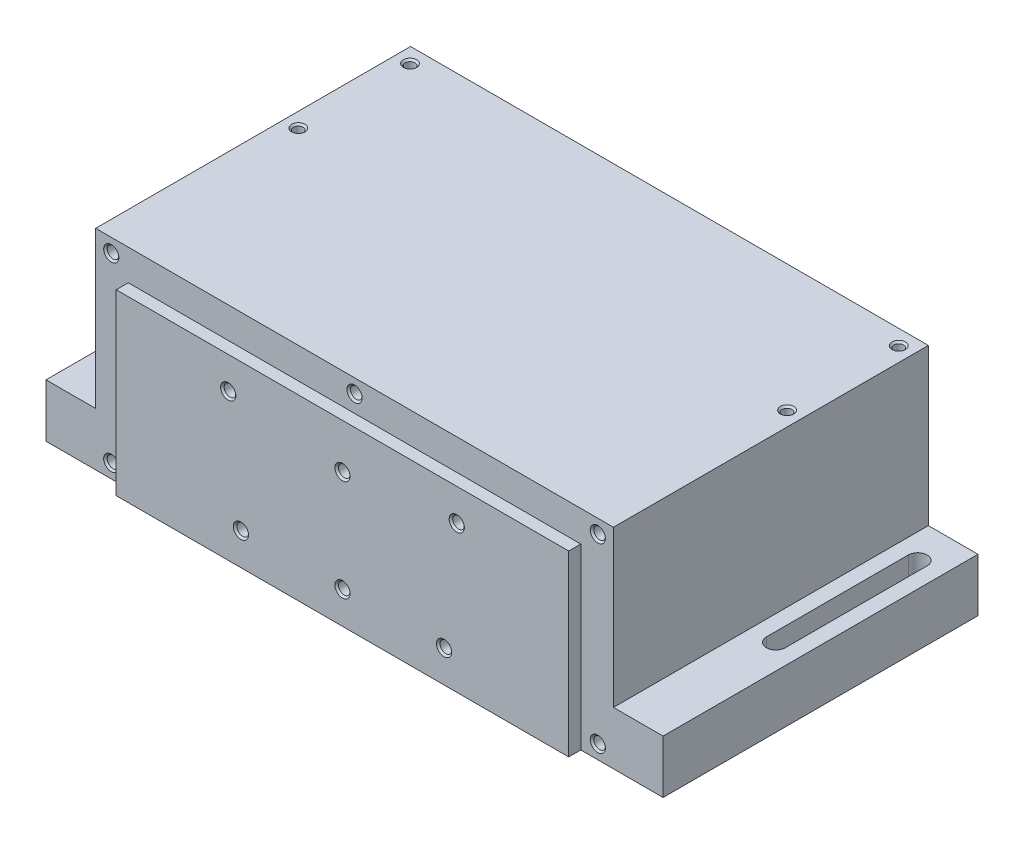
SolidWorks part; units mm, degrees
material "6061-T6 Al"
ref_plane "Front" through (0, 0, 0) normal (0, 0, 1) x (1, 0, 0)
ref_plane "Top" through (0, 0, 0) normal (0, 1, 0) x (1, 0, 0)
ref_plane "Right" through (0, 0, 0) normal (1, 0, 0) x (0, 0, -1)
sketch "Sketch1" plane through (0, 0, 0) normal (0, 0, 1) x (1, 0, 0)
  line L0 (-92.71, 2.54) -> (92.71, 2.54)
  line L1 (92.71, 2.54) -> (92.71, 0)
  line L2 (92.71, 0) -> (110.49, 0)
  line L3 (110.49, 0) -> (110.49, 19.05)
  line L4 (110.49, 19.05) -> (92.71, 19.05)
  line L5 (92.71, 19.05) -> (92.71, 74.93)
  line L6 (92.71, 74.93) -> (-92.71, 74.93)
  line L7 (0, 74.93) -> (0, 2.54) construction
  line L8 (-92.71, 19.05) -> (-92.71, 74.93)
  line L9 (-110.49, 19.05) -> (-92.71, 19.05)
  line L10 (-110.49, 0) -> (-110.49, 19.05)
  line L11 (-92.71, 0) -> (-110.49, 0)
  line L12 (-92.71, 2.54) -> (-92.71, 0)
  dimension "D1" = 220.98
  dimension "D3" = 2.54
  dimension "D4" = 185.42
  dimension "D5" = 19.05
  dimension "D6" = 74.93
extrude "Boss-Extrude1" add sketch "Sketch1" against normal blind 50.8
hole_wizard "#6-32 Tapped Hole1" positions "Sketch4" profile "Sketch3" tap size "#6-32" standard "ANSI Inch"
sketch "Sketch4" plane through (0, 74.93, 0) normal (0, 1, 0) x (1, 0, 0)
  line L0 (87.503, 45.4025) -> (0, 25.4) construction
  line L3 (0, 25.4) -> (-87.503, 5.3975) construction
  line L4 (0, 25.4) -> (92.71, 25.4) construction
  line L6 (92.71, 50.8) -> (92.71, 0) construction
  point P0 (-87.503, 45.4025)
  point P2 (-87.503, 5.3975)
  point P4 (87.503, 5.3975)
  point P6 (87.503, 45.4025)
  dimension "D1" = 175.006
  dimension "D2" = 40.005
sketch "Sketch3" plane through (-87.503, 74.93, -45.4025) normal (1, 0, 0) x (0, 0, 1)
  line L0 (0, 0) -> (0, 14.4271)
  line L1 (0, 14.4271) -> (1.3525, 13.6144)
  line L2 (1.3525, 13.6144) -> (1.3525, 9.652)
  line L3 (1.3525, 9.652) -> (1.7526, 9.652)
  line L5 (1.7526, 9.652) -> (1.7526, 0.635)
  line L6 (1.7526, 0.635) -> (2.3876, 0)
  line L7 (2.3876, 0) -> (0, 0)
  line L8 (-1.7526, 0.635) -> (-2.3876, 0) construction
  line L10 (0, 14.4271) -> (-1.3526, 13.6144) construction
  line L11 (0, -6.35) -> (0, 107.95) construction
  dimension "Tap Drill Dia." = 2.7051
  dimension "Tap Drill Depth" = 13.6144
  dimension "Thread Major Dia." = 3.5052
  dimension "Thread Depth" = 9.652
  dimension "Near C'Sink Dia." = 4.7752
  dimension "Near C'Sink Angle" = 90
  dimension "Drill Angle" = 118
sketch "Sketch5" plane through (0, 0, 0) normal (0, 0, 1) x (1, 0, 0)
  line L0 (0, 74.93) -> (0, 2.54) construction
  line L1 (0, 74.93) -> (0, 2.54) construction
  line L2 (92.71, 74.93) -> (-92.71, 74.93) construction
  line L3 (92.71, 74.93) -> (-92.71, 74.93)
  line L4 (92.71, 74.93) -> (92.71, 19.05)
  line L5 (110.49, 19.05) -> (110.49, 0)
  line L6 (-92.71, 19.05) -> (-92.71, 74.93)
  line L8 (-92.71, 74.93) -> (-92.71, 19.05) construction
  line L9 (-92.71, 19.05) -> (-110.49, 19.05) construction
  line L10 (-110.49, 19.05) -> (-110.49, 0) construction
  line L11 (-110.49, 0) -> (-92.71, 0) construction
  line L12 (-92.71, 19.05) -> (-110.49, 19.05)
  line L13 (-110.49, 19.05) -> (-110.49, 0)
  line L14 (-110.49, 0) -> (110.49, 0)
  line L15 (92.71, 19.05) -> (110.49, 19.05)
extrude "Boss-Extrude2" add sketch "Sketch5" along normal blind 61.976
sketch "Sketch16" plane through (0, 19.05, 0) normal (0, 1, 0) x (1, 0, 0)
  line L0 (0, 25.4) -> (0, 50.8) construction
  line L2 (-104.9782, 38.1) -> (-104.9782, -12.7)
  line L3 (-98.2218, 38.1) -> (-98.2218, -12.7)
  line L6 (-101.6, 38.1) -> (-101.6, 12.7) construction
  line L8 (-101.6, 12.7) -> (-101.6, -12.7) construction
  line L12 (104.9782, 38.1) -> (104.9782, -12.7)
  line L13 (98.2218, 38.1) -> (98.2218, -12.7)
  line L16 (92.71, 50.8) -> (-92.71, 50.8) construction
  line L17 (0, 25.4) -> (92.71, 25.4) construction
  arc A0 (-104.9782, 38.1) -> (-98.2218, 38.1) centre (-101.6, 38.1) cw
  arc A1 (-98.2218, -12.7) -> (-104.9782, -12.7) centre (-101.6, -12.7) cw
  arc A6 (98.2218, -12.7) -> (104.9782, -12.7) centre (101.6, -12.7) ccw
  arc A7 (104.9782, 38.1) -> (98.2218, 38.1) centre (101.6, 38.1) ccw
  dimension "D5" = 203.2
  dimension "D1" = 12.7
  dimension "D2" = 6.7564
  dimension "D4" = 50.8
extrude "Cut-Extrude2" cut sketch "Sketch16" against normal through all
hole_wizard "#8-32 Tapped Hole1" positions "Sketch12" profile "Sketch11" tap size "#8-32" standard "ANSI Inch"
sketch "Sketch12" plane through (0, 0, 61.976) normal (0, 0, 1) x (1, 0, 0)
  line L0 (0, 74.93) -> (0, 2.54) construction
  line L1 (0, 74.93) -> (0, 0) construction
  line L2 (0, 37.465) -> (-87.122, 37.465) construction
  line L3 (92.71, 74.93) -> (-92.71, 74.93) construction
  line L4 (-92.71, 74.93) -> (-92.71, 19.05) construction
  line L5 (-110.49, 0) -> (110.49, 0) construction
  line L6 (92.71, 74.93) -> (-92.71, 74.93) construction
  point P0 (-87.122, 69.977)
  point P2 (-87.122, 4.953)
  point P11 (87.122, 4.953)
  point P12 (87.122, 69.977)
  point P19 (0, 69.977)
  dimension "D1" = 4.953
  dimension "D2" = 5.588
  dimension "D3" = 65.024
  dimension "D4" = 174.244
  dimension "D5" = 4.953
sketch "Sketch11" plane through (-87.122, 69.977, 61.976) normal (1, 0, 0) x (0, -1, 0)
  line L0 (0, 0) -> (0, 17.7002)
  line L1 (0, 17.7002) -> (1.7272, 16.6624)
  line L2 (1.7272, 16.6624) -> (1.7272, 12.7)
  line L3 (1.7272, 12.7) -> (2.0828, 12.7)
  line L5 (2.0828, 12.7) -> (2.0828, 0.635)
  line L6 (2.0828, 0.635) -> (2.7178, 0)
  line L7 (2.7178, 0) -> (0, 0)
  line L8 (-2.0828, 0.635) -> (-2.7178, 0) construction
  line L10 (0, 17.7002) -> (-1.7272, 16.6624) construction
  line L11 (0, -6.35) -> (0, 107.95) construction
  dimension "Tap Drill Dia." = 3.4544
  dimension "Tap Drill Depth" = 16.6624
  dimension "Thread Major Dia." = 4.1656
  dimension "Thread Depth" = 12.7
  dimension "Near C'Sink Dia." = 5.4356
  dimension "Near C'Sink Angle" = 90
  dimension "Drill Angle" = 118
sketch "Sketch13" plane through (0, 0, 61.976) normal (0, 0, 1) x (1, 0, 0)
  line L0 (-81.026, 0) -> (-81.026, 63.881)
  line L2 (-81.026, 63.881) -> (81.026, 63.881)
  line L3 (81.026, 63.881) -> (81.026, 0)
  line L4 (81.026, 0) -> (-81.026, 0)
  line L5 (0, 63.881) -> (0, 0) construction
  line L6 (-110.49, 0) -> (110.49, 0) construction
  dimension "D1" = 6.096
  dimension "D2" = 6.096
extrude "Boss-Extrude4" add sketch "Sketch13" along normal blind 4.318
hole_wizard "#8-32 Tapped Hole2" positions "Sketch8" profile "Sketch7" tap size "#8-32" standard "ANSI Inch"
sketch "Sketch8" plane through (-53.4499, 7.476, 66.294) normal (0, 0, 1) x (1, 0, 0)
  line L0 (53.4499, 67.454) -> (53.4499, -4.936) construction
  line L1 (53.4499, 56.405) -> (53.4499, 44.9242) construction
  line L8 (134.4759, 56.405) -> (-27.5761, 56.405) construction
  line L13 (53.4499, 4.0048) -> (53.4499, -7.476) construction
  line L14 (134.4759, -7.476) -> (134.4759, 56.405) construction
  point P0 (12.5305, 44.9242)
  point P2 (17.0771, 4.0048)
  point P8 (89.8227, 4.0048)
  point P9 (94.3693, 44.9242)
  point P56 (53.4499, 4.0048)
  point P69 (53.4499, 40.3776)
  dimension "D1" = 40.9194
  dimension "D2" = 81.8388
  dimension "D3" = 4.5466
  dimension "D4" = 11.4808
  dimension "D5" = 36.3728
  dimension "D6" = 77.2922
  dimension "D7" = 40.9194
  dimension "D8" = 40.1066
sketch "Sketch7" plane through (-40.9194, 52.4002, 66.294) normal (1, 0, 0) x (0, -1, 0)
  line L0 (0, 0) -> (0, 17.7002)
  line L1 (0, 17.7002) -> (1.7272, 16.6624)
  line L2 (1.7272, 16.6624) -> (1.7272, 12.7)
  line L3 (1.7272, 12.7) -> (2.0828, 12.7)
  line L5 (2.0828, 12.7) -> (2.0828, 0.635)
  line L6 (2.0828, 0.635) -> (2.7178, 0)
  line L7 (2.7178, 0) -> (0, 0)
  line L8 (-2.0828, 0.635) -> (-2.7178, 0) construction
  line L10 (0, 17.7002) -> (-1.7272, 16.6624) construction
  line L11 (0, -6.35) -> (0, 107.95) construction
  dimension "Tap Drill Dia." = 3.4544
  dimension "Tap Drill Depth" = 16.6624
  dimension "Thread Major Dia." = 4.1656
  dimension "Thread Depth" = 12.7
  dimension "Near C'Sink Dia." = 5.4356
  dimension "Near C'Sink Angle" = 90
  dimension "Drill Angle" = 118
sketch "Sketch17" plane through (0, 2.54, 0) normal (0, -1, 0) x (1, 0, 0)
  line L0 (-92.71, 0) -> (92.71, 0) construction
  line L1 (-92.71, 0) -> (92.71, 0)
  line L2 (-92.71, 0) -> (-92.71, 49.403)
  line L3 (-83.185, 58.928) -> (83.185, 58.928)
  line L4 (92.71, 49.403) -> (92.71, 0)
  line L5 (-110.49, 61.976) -> (-81.026, 61.976) construction
  arc A0 (83.185, 58.928) -> (92.71, 49.403) centre (83.185, 49.403) cw
  arc A1 (-92.71, 49.403) -> (-83.185, 58.928) centre (-83.185, 49.403) cw
  dimension "D2" = 9.525
  dimension "D1" = 3.048
extrude "Cut-Extrude3" cut sketch "Sketch17" along normal through all
hole_wizard "1/4-20 Tapped Hole1" positions "Sketch19" profile "Sketch18" tap size "1/4-20" standard "ANSI Inch"
sketch "Sketch19" plane through (0, 0, -50.8) normal (0, 0, -1) x (-1, 0, 0)
  line L0 (-25.4, 38.1) -> (0, 38.1) construction
  line L1 (0, 38.1) -> (25.4, 38.1) construction
  line L2 (0, 38.1) -> (0, 2.54) construction
  line L3 (92.71, 2.54) -> (-92.71, 2.54) construction
  line L4 (-92.71, 0) -> (-110.49, 0) construction
  point P0 (-25.4, 38.1)
  point P2 (25.4, 38.1)
  dimension "D1" = 38.1
  dimension "D2" = 50.8
sketch "Sketch18" plane through (25.4, 38.1, -50.8) normal (1, 0, 0) x (0, 1, 0)
  line L0 (0, 0) -> (0, 20.5838)
  line L1 (0, 20.5838) -> (2.5527, 19.05)
  line L2 (2.5527, 19.05) -> (2.5527, 12.7)
  line L3 (2.5527, 12.7) -> (3.175, 12.7)
  line L5 (3.175, 12.7) -> (3.175, 0.762)
  line L6 (3.175, 0.762) -> (3.937, 0)
  line L7 (3.937, 0) -> (0, 0)
  line L8 (-3.175, 0.762) -> (-3.937, 0) construction
  line L10 (0, 20.5838) -> (-2.5527, 19.05) construction
  line L11 (0, -6.35) -> (0, 107.95) construction
  dimension "Tap Drill Dia." = 5.1054
  dimension "Tap Drill Depth" = 19.05
  dimension "Thread Major Dia." = 6.35
  dimension "Thread Depth" = 12.7
  dimension "Near C'Sink Dia." = 7.874
  dimension "Near C'Sink Angle" = 90
  dimension "Drill Angle" = 118
